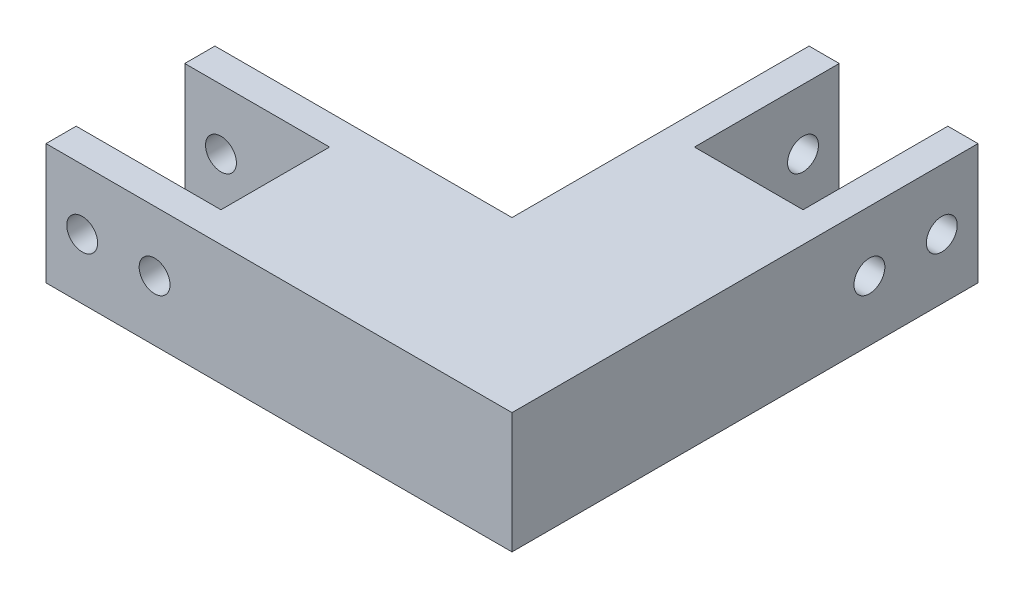
SolidWorks part; units mm, degrees
ref_plane "정면" through (0, 0, 0) normal (0, 0, 1) x (1, 0, 0)
ref_plane "윗면" through (0, 0, 0) normal (0, 1, 0) x (1, 0, 0)
ref_plane "우측면" through (0, 0, 0) normal (1, 0, 0) x (0, 0, -1)
sketch "스케치1" plane through (0, 0, 0) normal (0, 1, 0) x (1, 0, 0)
  line L0 (-17.5, 79.05) -> (-11.25, 79.05)
  line L1 (-11.25, 79.05) -> (-11.25, 49.05)
  line L2 (-11.25, 49.05) -> (11.25, 49.05)
  line L3 (11.25, 49.05) -> (11.25, 79.05)
  line L4 (11.25, 79.05) -> (17.5, 79.05)
  line L5 (17.5, 79.05) -> (17.5, -17.5)
  line L6 (17.5, -17.5) -> (-79.05, -17.5)
  line L7 (-79.05, -17.5) -> (-79.05, -11.25)
  line L8 (-79.05, -11.25) -> (-49.05, -11.25)
  line L9 (-49.05, -11.25) -> (-49.05, 11.25)
  line L10 (-49.05, 11.25) -> (-79.05, 11.25)
  line L11 (-79.05, 11.25) -> (-79.05, 17.5)
  line L12 (-79.05, 17.5) -> (-17.5, 17.5)
  line L13 (-17.5, 17.5) -> (-17.5, 79.05)
  point P14 (0, 49.05)
  point P16 (-15.41, 10.6884)
  point P17 (-21.8451, 6.5833)
  point P18 (-49.05, 0)
  point P19 (-15.5209, 16.125)
  point P20 (17.5, 54.3397)
  point P21 (-79.05, -14.375)
  point P22 (11.25, 24.8911)
  dimension "D1" = 22.5
  dimension "D2" = 22.5
  dimension "D3" = 35
  dimension "D4" = 35
  dimension "D5" = 30
  dimension "D6" = 30
  dimension "D7" = 49.05
  dimension "D8" = 49.05
extrude "보스-돌출1" add sketch "스케치1" along normal blind 25
sketch "스케치2" plane through (17.5, 0, 0) normal (1, 0, 0) x (0, 0, -1)
  line L0 (79.05, 25) -> (79.05, 0) construction
  line L1 (-17.5, 25) -> (79.05, 25) construction
  circle A0 centre (71.55, 12.5) radius 3.2
  circle A1 centre (56.55, 12.5) radius 3.2
  point P4 (0, 0)
  point P7 (0, 0)
  dimension "D3" = 6.4
  dimension "D1" = 15
  dimension "D2" = 7.5
  dimension "D4" = 12.5
extrude "컷-돌출1" cut sketch "스케치2" against normal up to surface (35 mm away) up to face at (-17.5, 12.5, -48.275)
sketch "스케치3" plane through (0, 0, 17.5) normal (0, 0, 1) x (1, 0, 0)
  line L0 (-79.05, 25) -> (-79.05, 0) construction
  line L1 (-79.05, 25) -> (17.5, 25) construction
  circle A0 centre (-71.55, 12.5) radius 3.2
  circle A1 centre (-56.55, 12.5) radius 3.2
  point P4 (0, 0)
  dimension "D2" = 6.4
  dimension "D1" = 15
  dimension "D3" = 7.5
  dimension "D4" = 12.5
extrude "컷-돌출2" cut sketch "스케치3" against normal up to surface (35 mm away) up to face at (-48.275, 12.5, -17.5)
